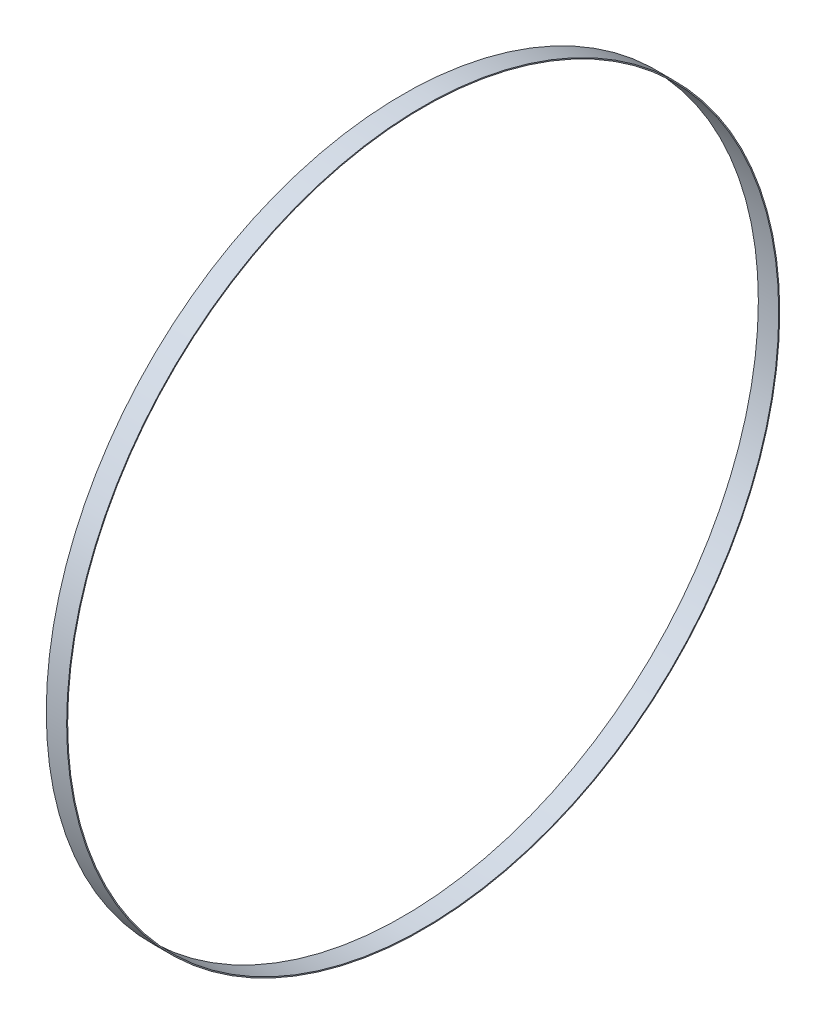
SolidWorks part; units mm, degrees
material "Malleable Cast Iron"
ref_plane "Front Plane" through (0, 0, 0) normal (0, 0, 1) x (1, 0, 0)
ref_plane "Top Plane" through (0, 0, 0) normal (0, 1, 0) x (1, 0, 0)
ref_plane "Right Plane" through (0, 0, 0) normal (1, 0, 0) x (0, 0, -1)
sketch "Sketch1" plane through (0, 0, 0) normal (1, 0, 0) x (0, 0, -1)
  circle A0 centre (0, 0) radius 17.5
  circle A1 centre (0, 0) radius 17.45
  dimension "D1" = 35
  dimension "D2" = 0.05
extrude "Boss-Extrude1" add sketch "Sketch1" along normal blind 1 contours A1
